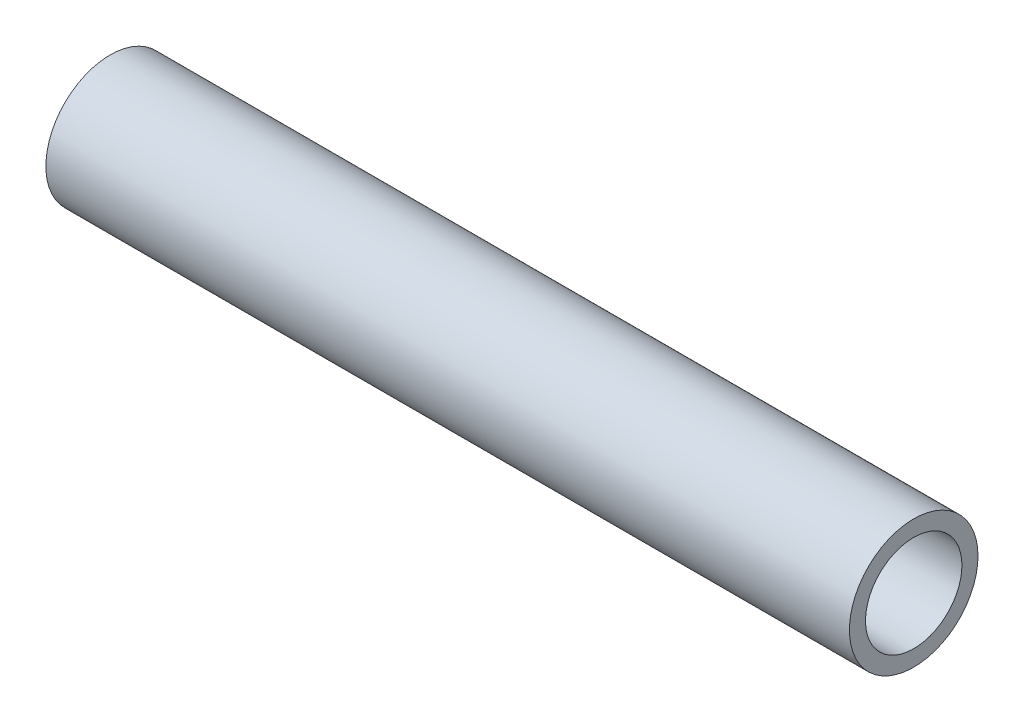
SolidWorks part; units mm, degrees
ref_plane "Front Plane" through (0, 0, 0) normal (0, 0, 1) x (1, 0, 0)
ref_plane "Top Plane" through (0, 0, 0) normal (0, 1, 0) x (1, 0, 0)
ref_plane "Right Plane" through (0, 0, 0) normal (1, 0, 0) x (0, 0, -1)
sketch "Sketch1" plane through (0, 0, 0) normal (1, 0, 0) x (0, 0, -1)
  circle A0 centre (0, 0) radius 1.5
  circle A1 centre (0, 0) radius 2
  dimension "D1" = 3
  dimension "D2" = 4
extrude "Boss-Extrude1" add sketch "Sketch1" along normal blind 25
